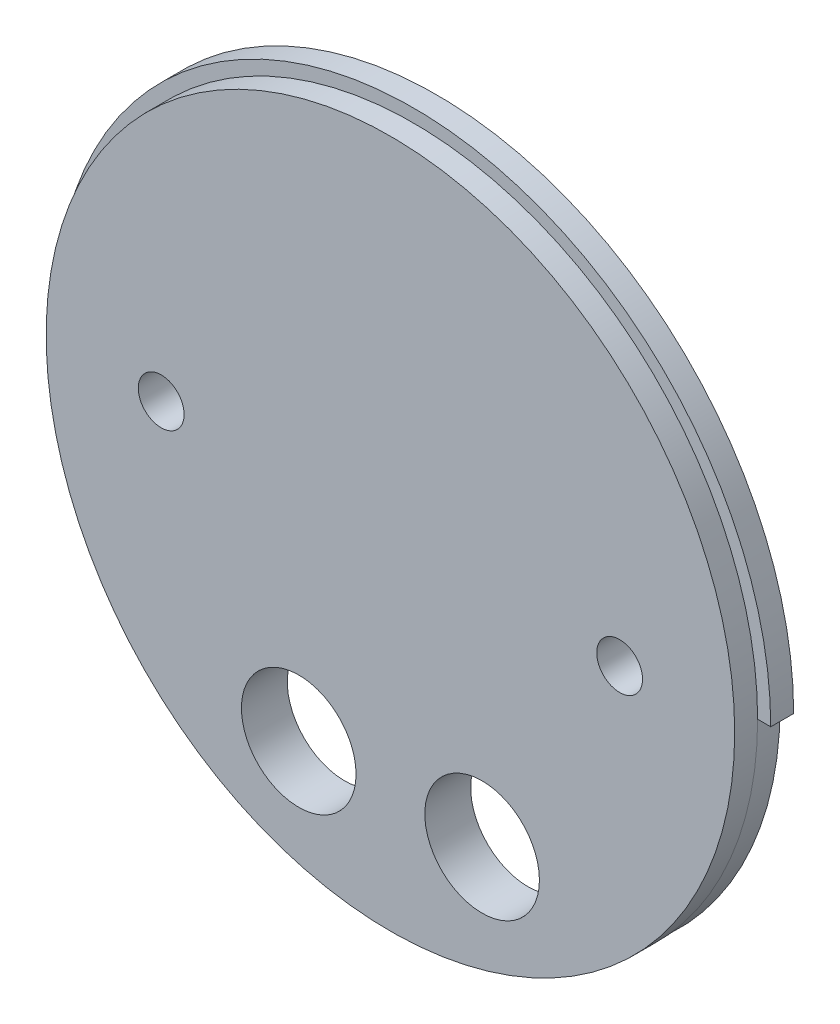
SolidWorks part; units mm, degrees
ref_plane "Front Plane" through (0, 0, 0) normal (0, 0, 1) x (1, 0, 0)
ref_plane "Top Plane" through (0, 0, 0) normal (0, 1, 0) x (1, 0, 0)
ref_plane "Right Plane" through (0, 0, 0) normal (1, 0, 0) x (0, 0, -1)
sketch "Sketch1" plane through (0, 0, 0) normal (0, 0, 1) x (1, 0, 0)
  circle A0 centre (0, 0) radius 49.5046
  dimension "D1" = 99.0092
extrude "Boss-Extrude1" add sketch "Sketch1" along normal blind 3.175
sketch "Sketch2" plane through (0, 0, 3.175) normal (0, 0, 1) x (1, 0, 0)
  circle A0 centre (0, 0) radius 47.6885
  dimension "D1" = 95.377
extrude "Boss-Extrude2" add sketch "Sketch2" along normal blind 3.175
sketch "Sketch3" plane through (0, 0, 6.35) normal (0, 0, 1) x (1, 0, 0)
  line L0 (-7.9375, -31.2354) -> (7.9375, -31.2354) construction
  circle A0 centre (-31.75, 0) radius 3.175
  circle A1 centre (31.75, 0) radius 3.175
  circle A2 centre (-12.7, -31.2354) radius 7.9375
  circle A3 centre (-12.7, -31.2354) radius 13.97 construction
  circle A4 centre (-12.7, -31.2354) radius 4.7625 construction
  circle A5 centre (0, 0) radius 47.6885 construction
  circle A6 centre (12.7, -31.2354) radius 7.9375
  circle A7 centre (12.7, -31.2354) radius 13.97 construction
  circle A8 centre (-12.7, -31.2354) radius 12.7 construction
  circle A9 centre (12.7, -31.2354) radius 12.7 construction
  circle A10 centre (12.7, -31.2354) radius 4.7625 construction
  dimension "D1" = 6.35
  dimension "D2" = 6.35
  dimension "D5" = 15.875
  dimension "D6" = 27.94
  dimension "D7" = 15.875
  dimension "D8" = 27.94
  dimension "D9" = 25.4
  dimension "D10" = 25.4
  dimension "D11" = 9.525
  dimension "D12" = 9.525
  dimension "D3" = 63.5
  dimension "D4" = 31.75
extrude "Cut-Extrude1" cut sketch "Sketch3" against normal through all
sketch "Sketch4" plane through (0, 0, 3.175) normal (0, 0, 1) x (1, 0, 0)
  line L0 (-50.165, 0) -> (-47.625, 0)
  line L1 (47.625, 0) -> (50.165, 0)
  arc A0 (-50.165, 0) -> (50.165, 0) centre (0, 0) ccw
  arc A1 (-47.625, 0) -> (47.625, 0) centre (0, 0) ccw
extrude "Cut-Extrude2" cut sketch "Sketch4" against normal through all
